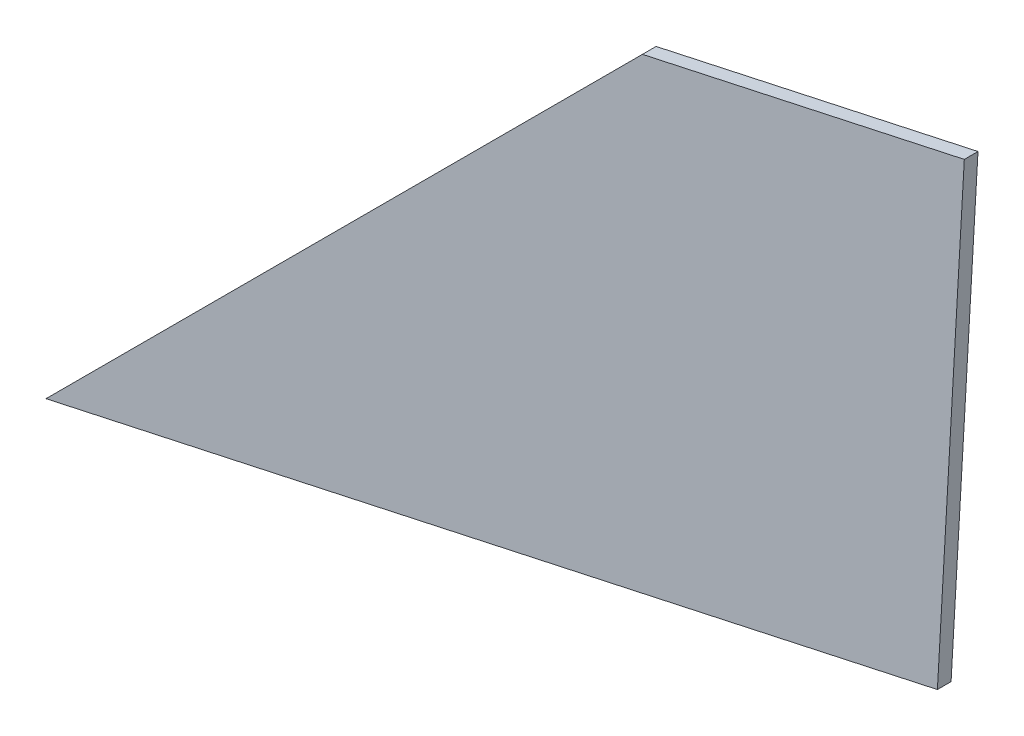
SolidWorks part; units mm, degrees
ref_plane "Front Plane" through (0, 0, 0) normal (0, 0, 1) x (1, 0, 0)
ref_plane "Top Plane" through (0, 0, 0) normal (0, 1, 0) x (1, 0, 0)
ref_plane "Right Plane" through (0, 0, 0) normal (1, 0, 0) x (0, 0, -1)
sketch "Sketch1" plane through (0, 0, 0) normal (0, 0, 1) x (1, 0, 0)
  line L0 (0, 0) -> (175.8917, 38.2373)
  line L1 (175.8917, 38.2373) -> (181.2025, 131.4939)
  line L2 (181.2025, 131.4939) -> (117.686, 117.686)
  line L3 (117.686, 117.686) -> (0, 0)
  line L4 (0, 0) -> (0, 37.2528) construction
  dimension "D1" = 180
  dimension "D2" = 90
  dimension "D3" = 166.4332
  dimension "D4" = 65
  dimension "D5" = 147.265
  dimension "D6" = 45
extrude "Boss-Extrude1" add sketch "Sketch1" along normal blind 2.7
